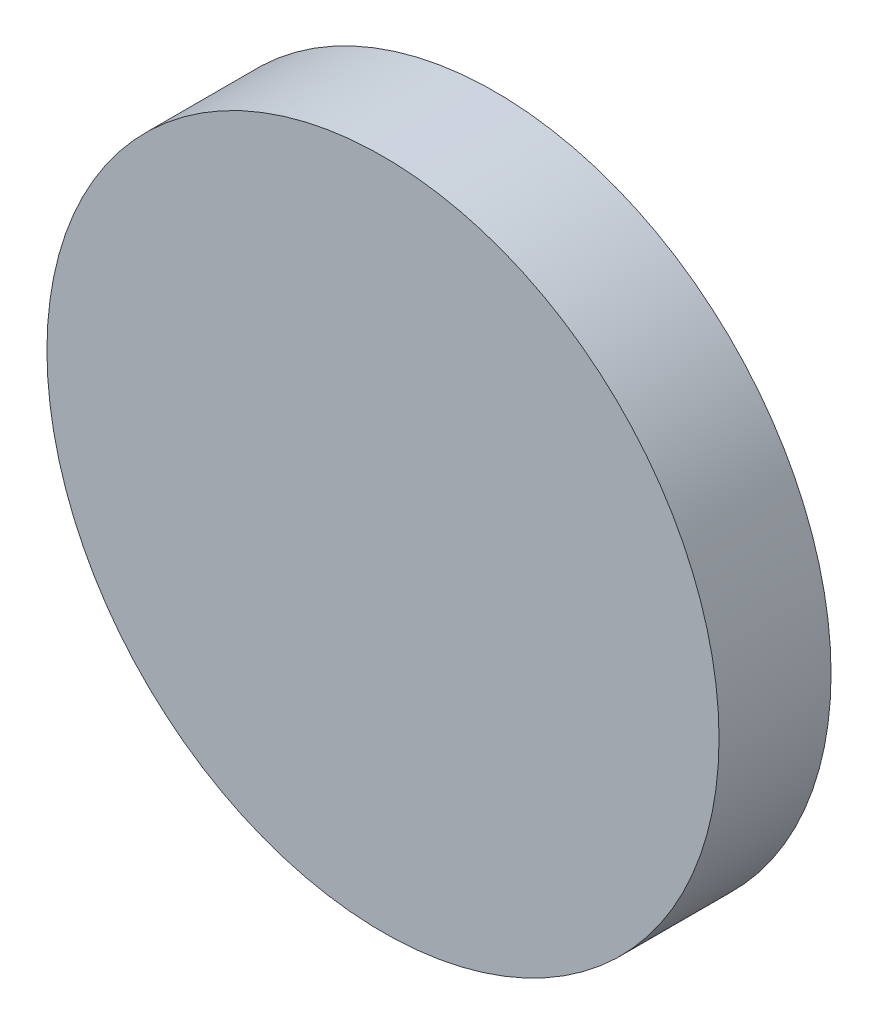
SolidWorks part; units mm, degrees
ref_plane "Front Plane" through (0, 0, 0) normal (0, 0, 1) x (1, 0, 0)
ref_plane "Top Plane" through (0, 0, 0) normal (0, 1, 0) x (1, 0, 0)
ref_plane "Right Plane" through (0, 0, 0) normal (1, 0, 0) x (0, 0, -1)
sketch "Sketch1" plane through (0, 0, 0) normal (0, 0, 1) x (1, 0, 0)
  line L0 (0, 0) -> (-12.6313, 0) construction
  line L1 (-12.6313, 0) -> (12.3827, 0) construction
  line L2 (12.3827, 0) -> (0, 0) construction
  line L3 (0, 0) -> (0, 12.3081) construction
  line L4 (0, 12.3081) -> (0, -7.2357) construction
  circle A0 centre (0, 0) radius 3
  dimension "D1" = 6
extrude "Boss-Extrude1" add sketch "Sketch1" along normal blind 1
sketch "Sketch2" plane through (0, 0, 1) normal (0, 0, 1) x (1, 0, 0)
  circle A0 centre (0, 0) radius 2
  dimension "D1" = 4
sketch "Sketch3" plane through (0, 0, 0) normal (0, 0, -1) x (-1, 0, 0)
  circle A0 centre (0, 0) radius 2
  dimension "D1" = 4
